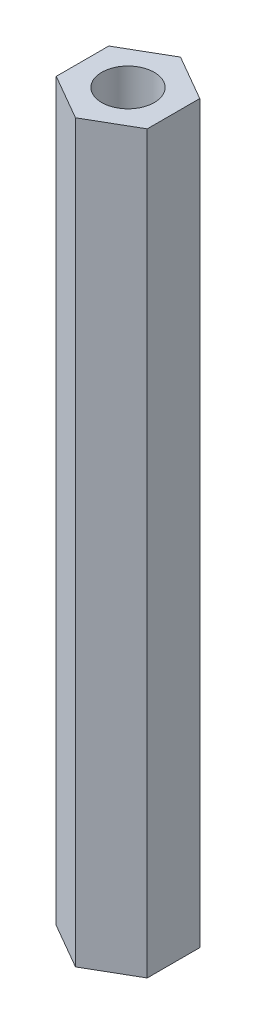
SolidWorks part; units mm, degrees
ref_plane "Face" through (0, 0, 0) normal (0, 0, 1) x (1, 0, 0)
ref_plane "Dessus" through (0, 0, 0) normal (0, 1, 0) x (1, 0, 0)
ref_plane "Droite" through (0, 0, 0) normal (1, 0, 0) x (0, 0, -1)
sketch "Esquisse1" plane through (0, 0, 0) normal (0, 1, 0) x (1, 0, 0)
  line L0 (0, 0) -> (0, 5.5688) construction
  line L1 (0, 5) -> (-4.3301, 2.5)
  line L2 (-4.3301, 2.5) -> (-4.3301, -2.5)
  line L3 (-4.3301, -2.5) -> (0, -5)
  line L4 (0, -5) -> (4.3301, -2.5)
  line L5 (4.3301, -2.5) -> (4.3301, 2.5)
  line L6 (4.3301, 2.5) -> (0, 5)
  circle A0 centre (0, 0) radius 4.3301 construction
  circle A1 centre (0, 0) radius 2.5
  dimension "D1" = 10
  dimension "D2" = 5
extrude "Extrusion1" add sketch "Esquisse1" along normal blind 70
